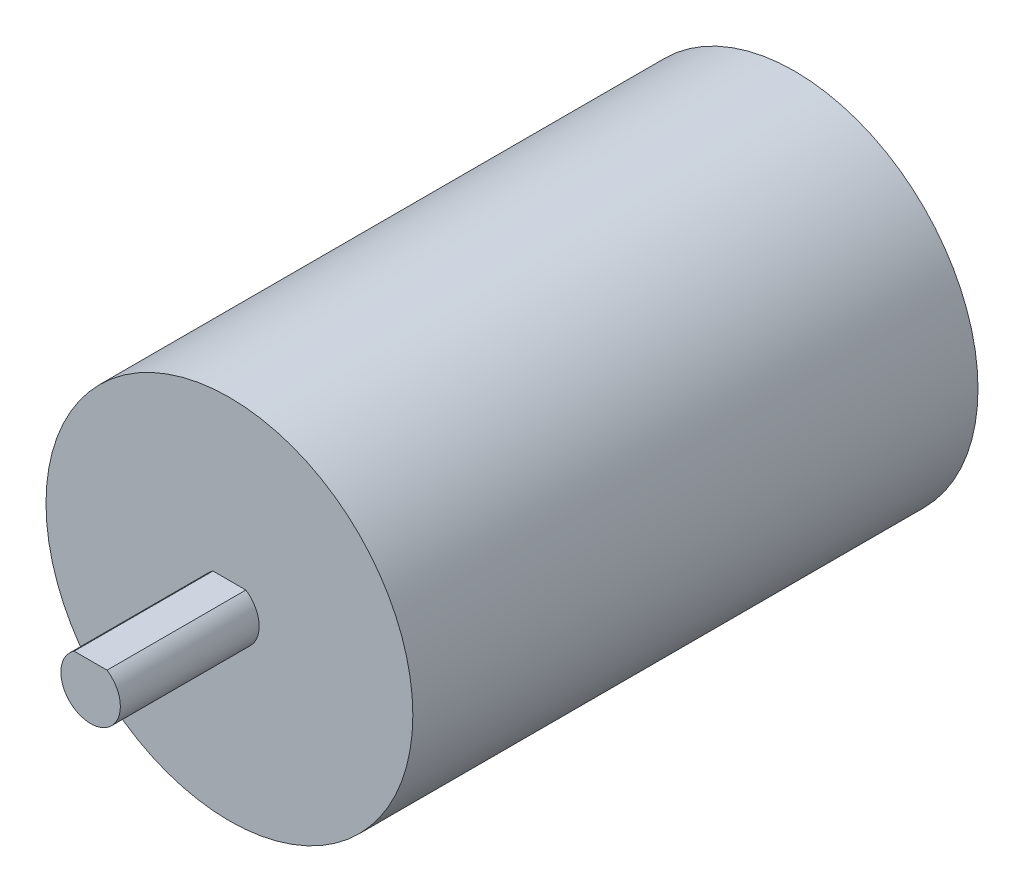
SolidWorks part; units mm, degrees
ref_plane "Front Plane" through (0, 0, 0) normal (0, 0, 1) x (1, 0, 0)
ref_plane "Top Plane" through (0, 0, 0) normal (0, 1, 0) x (1, 0, 0)
ref_plane "Right Plane" through (0, 0, 0) normal (1, 0, 0) x (0, 0, -1)
sketch "Sketch1" plane through (0, 0, 0) normal (0, 0, 1) x (1, 0, 0)
  circle A0 centre (0, 0) radius 18.5
  dimension "D1" = 37
extrude "Boss-Extrude1" add sketch "Sketch1" along normal blind 57
sketch "Sketch2" plane through (0, 0, 57) normal (0, 0, 1) x (1, 0, 0)
  line L0 (-1.6583, 2.5) -> (1.6583, 2.5)
  circle A0 centre (0, 0) radius 3
  point P5 (0, -3)
  dimension "D1" = 6
  dimension "D2" = 5.5
extrude "Boss-Extrude2" add sketch "Sketch2" along normal blind 14 contours L0 A0
